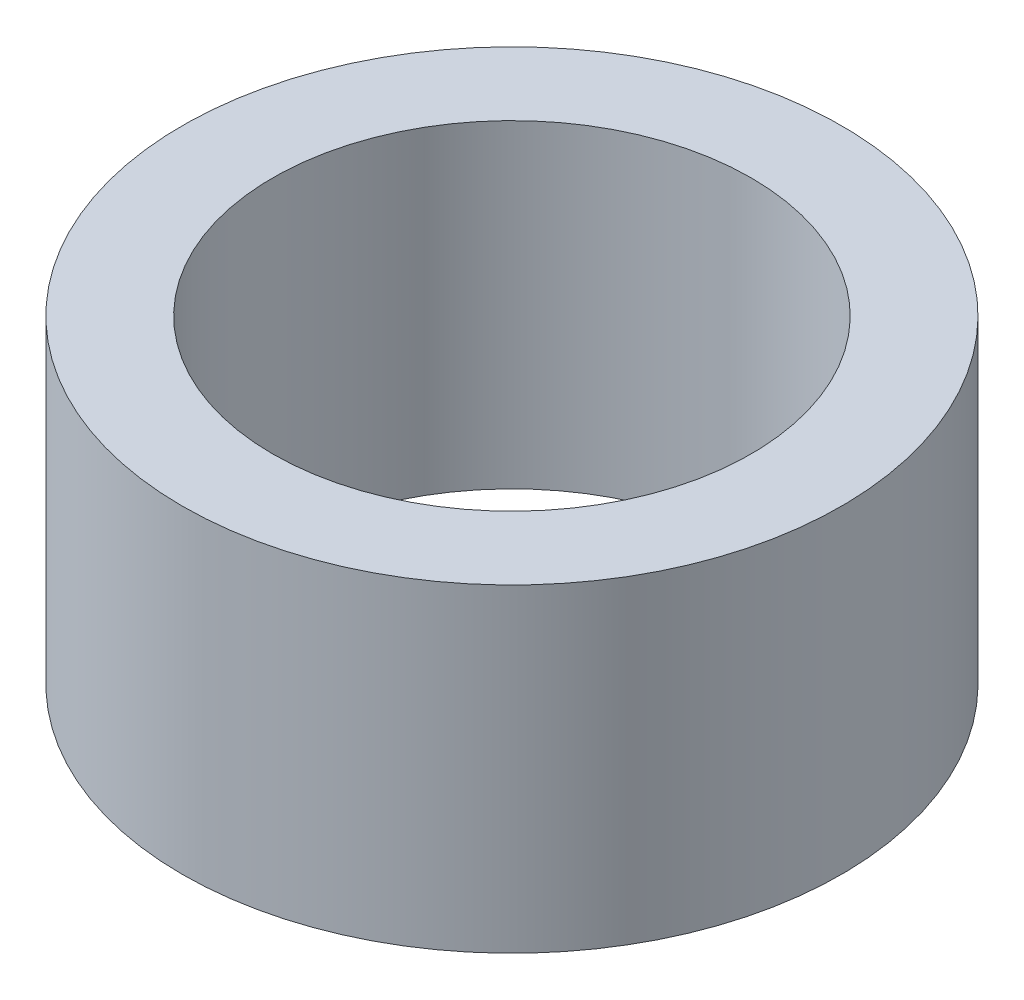
SolidWorks part; units mm, degrees
ref_plane "Front Plane" through (0, 0, 0) normal (0, 0, 1) x (1, 0, 0)
ref_plane "Top Plane" through (0, 0, 0) normal (0, 1, 0) x (1, 0, 0)
ref_plane "Right Plane" through (0, 0, 0) normal (1, 0, 0) x (0, 0, -1)
sketch "Sketch1" plane through (0, 0, 0) normal (0, 1, 0) x (1, 0, 0)
  circle A0 centre (0, 0) radius 3.1
  circle A1 centre (0, 0) radius 2.25
  dimension "D1" = 4.5
  dimension "D2" = 6.2
extrude "Boss-Extrude1" add sketch "Sketch1" along normal blind 3
